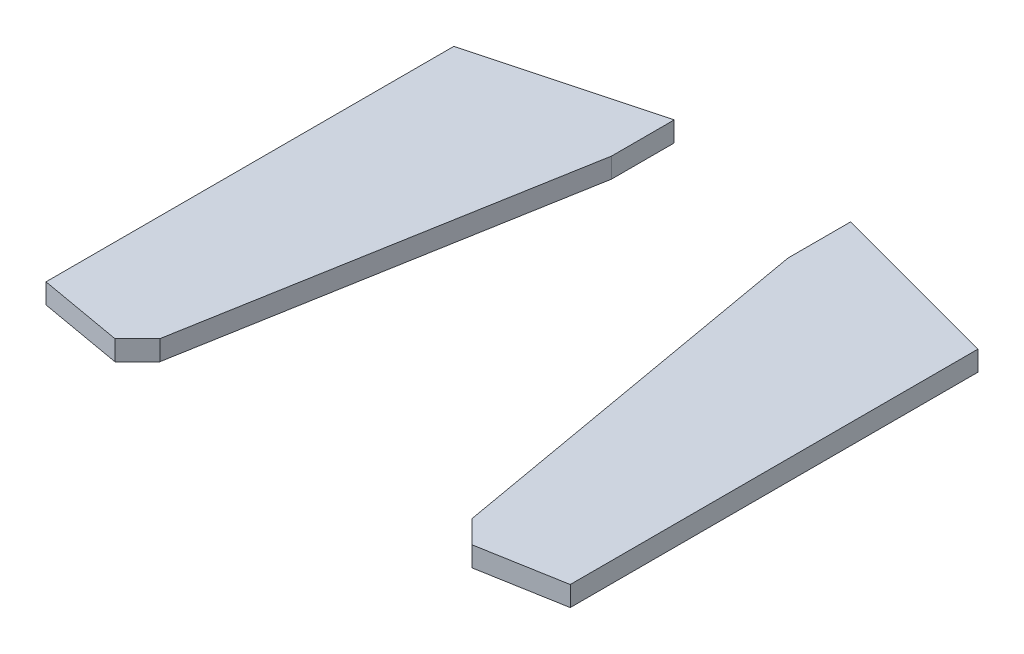
SolidWorks part; units mm, degrees
ref_plane "Front Plane" through (0, 0, 0) normal (0, 0, 1) x (1, 0, 0)
ref_plane "Top Plane" through (0, 0, 0) normal (0, 1, 0) x (1, 0, 0)
ref_plane "Right Plane" through (0, 0, 0) normal (1, 0, 0) x (0, 0, -1)
sketch "Sketch1" plane through (0, 0, 0) normal (0, 1, 0) x (1, 0, 0)
  line L0 (-585.1341, -719.7383) -> (-331.1737, 720.5431)
  line L1 (-331.1737, 720.5431) -> (-0.1341, 720.5431)
  line L2 (-0.1341, 720.5431) -> (-0.1341, -719.7383) construction
  line L3 (584.8659, -719.7383) -> (330.9054, 720.5431)
  line L4 (-0.1341, 720.5431) -> (330.9054, 720.5431)
  line L5 (-585.1341, -719.7383) -> (-0.1341, -719.7383)
  line L6 (-0.1341, -719.7383) -> (584.8659, -719.7383)
sketch "Sketch2" plane through (0, 0, 0) normal (0, 1, 0) x (1, 0, 0)
  line L0 (7880.6911, 7713.8107) -> (8543.3578, 7713.8107) construction
  line L1 (584.8659, -719.7383) -> (668.9578, -803.8302)
  line L6 (330.9054, 720.5431) -> (584.8659, -719.7383)
  line L7 (330.9054, 720.5431) -> (330.9054, 955.4467)
  line L9 (668.9578, -803.8302) -> (982.9281, -748.4688)
  line L10 (982.9281, -748.4688) -> (982.9281, 780.7378)
  line L11 (982.9281, 780.7378) -> (330.9054, 955.4467)
  line L12 (-0.1341, -719.7383) -> (-0.1341, 720.5431) construction
  line L13 (-331.1737, 720.5431) -> (-331.1737, 955.4467)
  line L14 (-983.1963, 780.7378) -> (-331.1737, 955.4467)
  line L15 (-983.1963, -748.4688) -> (-983.1963, 780.7378)
  line L16 (-669.2261, -803.8302) -> (-983.1963, -748.4688)
  line L17 (-585.1341, -719.7383) -> (-669.2261, -803.8302)
  line L18 (-331.1737, 720.5431) -> (-585.1341, -719.7383)
extrude "Boss-Extrude1" add sketch "Sketch2" along normal blind 75 contours L15 L14 L13 L18 L17 L16 | L11 L7 L6 L1 L9 L10
